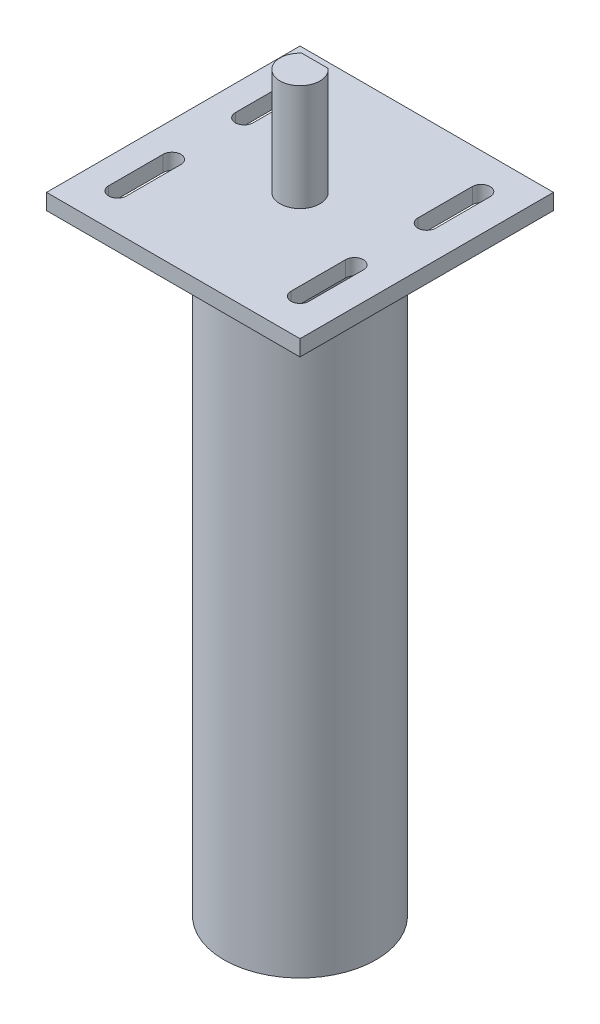
SolidWorks part; units mm, degrees
material "Plain Carbon Steel"
ref_plane "Front Plane" through (0, 0, 0) normal (0, 0, 1) x (1, 0, 0)
ref_plane "Top Plane" through (0, 0, 0) normal (0, 1, 0) x (1, 0, 0)
ref_plane "Right Plane" through (0, 0, 0) normal (1, 0, 0) x (0, 0, -1)
sketch "Sketch1" plane through (0, 0, 0) normal (0, 1, 0) x (1, 0, 0)
  circle A0 centre (0, 0) radius 15.24
  dimension "D1" = 30.48
extrude "Boss-Extrude1" add sketch "Sketch1" along normal blind 122.428
sketch "Sketch2" plane through (0, 122.428, 0) normal (0, 1, 0) x (1, 0, 0)
  line L0 (0, 0) -> (0, 11.3458) construction
  line L1 (-25.4, 25.4) -> (25.4, 25.4)
  line L2 (-25.4, 25.4) -> (-25.4, -25.4)
  line L3 (-25.4, -25.4) -> (25.4, -25.4)
  line L4 (25.4, 25.4) -> (25.4, -25.4)
  line L5 (-25.4, 25.4) -> (25.4, -25.4) construction
  line L6 (-25.4, -25.4) -> (25.4, 25.4) construction
  point P0 (0, 0)
  dimension "D1" = 50.8
  dimension "D2" = 50.8
extrude "Boss-Extrude2" add sketch "Sketch2" along normal blind 3.175
sketch "Sketch3" plane through (0, 125.603, 0) normal (0, 1, 0) x (1, 0, 0)
  circle A0 centre (0, 0) radius 4
  dimension "D1" = 8
extrude "Boss-Extrude3" add sketch "Sketch3" along normal blind 21.336
sketch "Sketch4" plane through (0, 146.939, 0) normal (0, 1, 0) x (1, 0, 0)
  line L0 (0, -4) -> (0, 3) construction
  line L1 (2.6458, 3) -> (-2.6458, 3)
  circle A0 centre (0, 0) radius 4 construction
  arc A1 (2.6458, 3) -> (-2.6458, 3) centre (0, 0) ccw
  dimension "D1" = 7
extrude "Cut-Extrude1" cut sketch "Sketch4" against normal up to surface (21.336 mm away) up to face at (0, 125.603, 4)
sketch "Sketch5" plane through (0, 125.603, 0) normal (0, 1, 0) x (1, 0, 0)
  line L0 (-18.542, 18.288) -> (-18.542, 7.366) construction
  line L1 (-16.764, 18.288) -> (-16.764, 7.366)
  line L2 (-20.32, 18.288) -> (-20.32, 7.366)
  line L3 (25.4, 25.4) -> (-25.4, 25.4) construction
  line L4 (-25.4, 25.4) -> (-25.4, -25.4) construction
  line L5 (-18.542, -7.112) -> (-18.542, -18.034) construction
  line L6 (-16.764, -7.112) -> (-16.764, -18.034)
  line L7 (-20.32, -7.112) -> (-20.32, -18.034)
  line L8 (18.034, -7.112) -> (18.034, -18.034) construction
  line L9 (19.812, -7.112) -> (19.812, -18.034)
  line L10 (16.256, -7.112) -> (16.256, -18.034)
  line L11 (18.034, 18.288) -> (18.034, 7.366) construction
  line L12 (19.812, 18.288) -> (19.812, 7.366)
  line L13 (16.256, 18.288) -> (16.256, 7.366)
  arc A0 (-16.764, 18.288) -> (-20.32, 18.288) centre (-18.542, 18.288) ccw
  arc A1 (-20.32, 7.366) -> (-16.764, 7.366) centre (-18.542, 7.366) ccw
  arc A2 (-16.764, -7.112) -> (-20.32, -7.112) centre (-18.542, -7.112) ccw
  arc A3 (-20.32, -18.034) -> (-16.764, -18.034) centre (-18.542, -18.034) ccw
  arc A4 (19.812, -7.112) -> (16.256, -7.112) centre (18.034, -7.112) ccw
  arc A5 (16.256, -18.034) -> (19.812, -18.034) centre (18.034, -18.034) ccw
  arc A6 (19.812, 18.288) -> (16.256, 18.288) centre (18.034, 18.288) ccw
  arc A7 (16.256, 7.366) -> (19.812, 7.366) centre (18.034, 7.366) ccw
  point P2 (-18.542, 12.827)
  point P15 (-18.542, -12.573)
  point P22 (18.034, -12.573)
  point P29 (18.034, 12.827)
  dimension "D3" = 1.778
  dimension "D1" = 7.112
  dimension "D2" = 6.858
  dimension "D4" = 10.922
  dimension "D5" = 2
  dimension "D6" = 2
extrude "Cut-Extrude2" cut sketch "Sketch5" against normal up to surface (3.175 mm away) up to face at (0, 122.428, 15.24)
sketch "Sketch6" plane through (0, 125.603, 0) normal (0, 1, 0) x (1, 0, 0)
  line L0 (18.034, 12.827) -> (-18.542, 12.827) construction
  line L1 (-18.542, 12.827) -> (-18.542, -12.573) construction
  line L2 (-18.542, -12.573) -> (18.034, -12.573) construction
  line L3 (18.034, -12.573) -> (18.034, 12.827) construction
  dimension "D1" = 36.576
  dimension "D2" = 25.4
